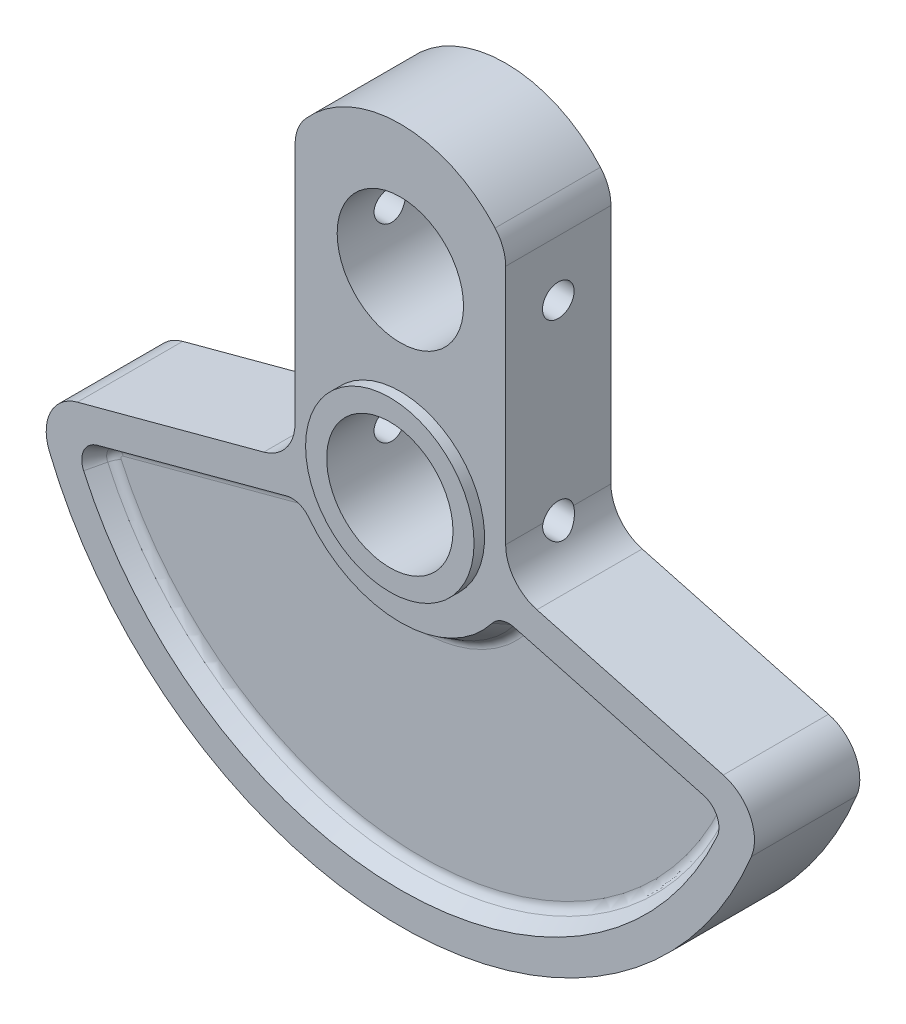
SolidWorks part; units mm, degrees
ref_plane "Front Plane" through (0, 0, 0) normal (0, 0, 1) x (1, 0, 0)
ref_plane "Top Plane" through (0, 0, 0) normal (0, 1, 0) x (1, 0, 0)
ref_plane "Right Plane" through (0, 0, 0) normal (1, 0, 0) x (0, 0, -1)
sketch "Sketch1" plane through (0, 0, 0) normal (0, 0, 1) x (1, 0, 0)
  line L0 (-10, 23.2915) -> (-10, 0.3898)
  line L1 (10, 23.2915) -> (10, 0.3898)
  line L2 (-12.9647, -3.4739) -> (-30.6672, -8.2172)
  line L4 (0, 32.1199) -> (0, -32.1199) construction
  line L5 (12.9647, -3.4739) -> (30.6672, -8.2172)
  circle A0 centre (0, 0) radius 6
  circle A1 centre (0, 18) radius 6
  arc A2 (-33.3359, -13.5911) -> (33.3359, -13.5911) centre (0, 0) ccw
  arc A4 (9, 25.9373) -> (-9, 25.9373) centre (0, 18) ccw
  arc A5 (-10, 23.2915) -> (-9, 25.9373) centre (-6, 23.2915) cw
  arc A6 (10, 23.2915) -> (9, 25.9373) centre (6, 23.2915) ccw
  arc A7 (30.6672, -8.2172) -> (33.3359, -13.5911) centre (29.6319, -12.081) cw
  arc A8 (10, 0.3898) -> (12.9647, -3.4739) centre (14, 0.3898) ccw
  arc A9 (-10, 0.3898) -> (-12.9647, -3.4739) centre (-14, 0.3898) cw
  arc A10 (-30.6672, -8.2172) -> (-33.3359, -13.5911) centre (-29.6319, -12.081) ccw
  point P9 (0, 0)
  point P14 (0, 0)
  point P16 (0, 30)
  point P24 (10, -2.6795)
  point P27 (-10, -2.6795)
  dimension "D1" = 12
  dimension "D3" = 72
  dimension "D4" = 75
  dimension "D7" = 4
  dimension "D2" = 18
  dimension "D5" = 10
  dimension "D6" = 10
  dimension "D8" = 30
extrude "Boss-Extrude1" add sketch "Sketch1" along normal mid plane 10
sketch "Sketch2" plane through (0, 0, 5) normal (0, 0, 1) x (1, 0, 0)
  line L0 (30.6672, -8.2172) -> (12.9647, -3.4739) construction
  line L1 (-12.9647, -3.4739) -> (-30.6672, -8.2172) construction
  line L2 (30.6672, -8.2172) -> (12.9647, -3.4739) construction
  line L3 (-12.9647, -3.4739) -> (-30.6672, -8.2172) construction
  line L4 (-28.7752, -10.8161) -> (-10.8147, -6.0036)
  line L5 (28.7752, -10.8161) -> (10.8147, -6.0036)
  arc A0 (-30.0806, -13.5704) -> (30.0806, -13.5704) centre (0, 0) ccw
  arc A1 (-33.3359, -13.5911) -> (33.3359, -13.5911) centre (0, 0) ccw construction
  circle A2 centre (0, 0) radius 6 construction
  circle A3 centre (0, 0) radius 6 construction
  arc A4 (-8.7129, -6.7146) -> (8.7129, -6.7146) centre (0, 0) ccw
  arc A5 (28.7752, -10.8161) -> (30.0806, -13.5704) centre (28.2576, -12.748) cw
  arc A6 (10.8147, -6.0036) -> (8.7129, -6.7146) centre (10.297, -7.9355) ccw
  arc A7 (-10.8147, -6.0036) -> (-8.7129, -6.7146) centre (-10.297, -7.9355) cw
  arc A8 (-28.7752, -10.8161) -> (-30.0806, -13.5704) centre (-28.2576, -12.748) ccw
  point P16 (0, 0)
  dimension "D1" = 3
  dimension "D3" = 5
  dimension "D5" = 2
  dimension "D2" = 3
  dimension "D4" = 3
extrude "Cut-Extrude1" cut sketch "Sketch2" against normal blind 2 draft 30
fillet "Fillet1" radius 1 8 edges at (29.0214, -12.3859, 3) (0, -31.8453, 3) (-29.0214, -12.3859, 3) (-19.4961, -9.5252, 3) (-10.0261, -7.1347, 3) (0, -12.1547, 3) (10.0261, -7.1347, 3) (19.4961, -9.5252, 3)
mirror "Mirror2" about plane through (0, 0, 0) normal (0, 0, 1) of "Cut-Extrude1", "Fillet1"
sketch "Sketch3" plane through (0, 0, -5) normal (0, 0, -1) x (-1, 0, 0)
  circle A0 centre (0, 18) radius 6 construction
  circle A1 centre (0, 18) radius 6
  circle A2 centre (0, 18) radius 8
  dimension "D1" = 16
extrude "Boss-Extrude2" add sketch "Sketch3" along normal blind 1
sketch "Sketch4" plane through (0, 0, 5) normal (0, 0, 1) x (1, 0, 0)
  circle A0 centre (0, 0) radius 6 construction
  circle A1 centre (0, 0) radius 6
  circle A2 centre (0, 0) radius 8
  dimension "D1" = 16
extrude "Boss-Extrude3" add sketch "Sketch4" along normal blind 1
sketch "Sketch5" plane through (-10, 0, 0) normal (-1, 0, 0) x (0, 0, 1)
  circle A0 centre (0, 18) radius 1.5
  circle A1 centre (0, 0) radius 1.5
  point P5 (0, 0)
  point P6 (0, 0)
  point P7 (0, 0)
  dimension "D1" = 3
  dimension "D2" = 18
extrude "Cut-Extrude2" cut sketch "Sketch5" against normal through all
